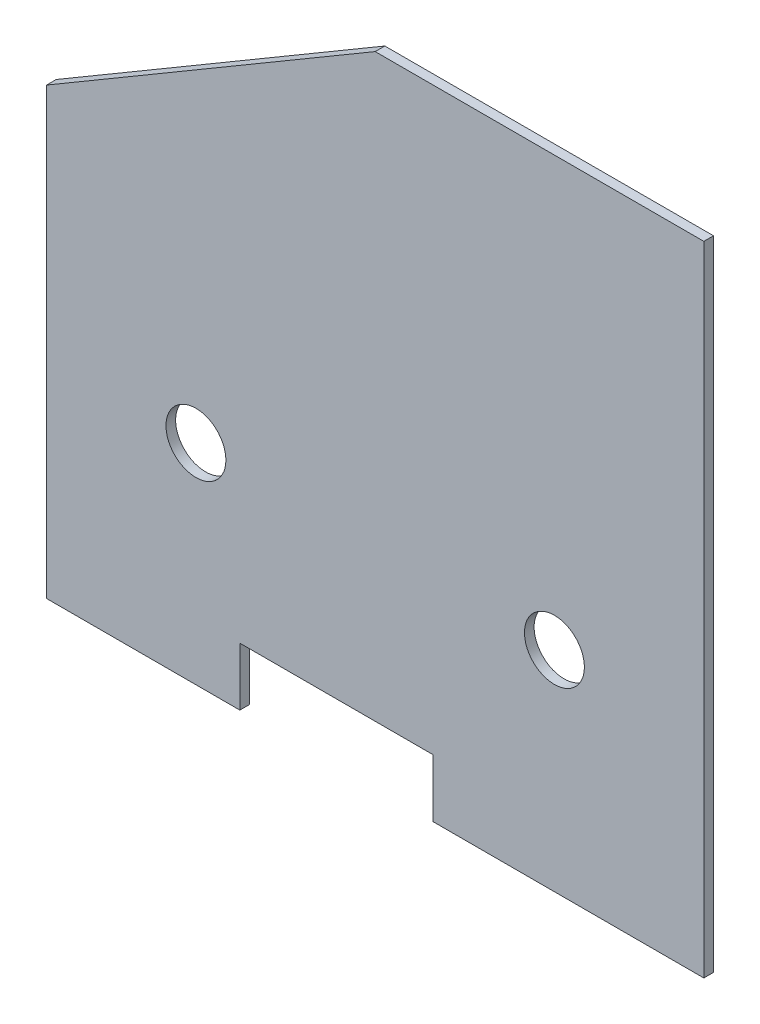
SolidWorks part; units mm, degrees
ref_plane "Front Plane" through (0, 0, 0) normal (0, 0, 1) x (1, 0, 0)
ref_plane "Top Plane" through (0, 0, 0) normal (0, 1, 0) x (1, 0, 0)
ref_plane "Right Plane" through (0, 0, 0) normal (1, 0, 0) x (0, 0, -1)
sketch "Sketch2" plane through (0, 0, 0) normal (0, 0, 1) x (1, 0, 0)
  line L0 (0, 304.8) -> (0, 12.7)
  line L1 (0, 0) -> (431.8, 0) construction
  line L2 (0, 0) -> (0, 431.8) construction
  line L3 (0, 431.8) -> (431.8, 431.8) construction
  line L4 (431.8, 0) -> (431.8, 431.8) construction
  line L5 (0, 304.8) -> (215.9, 431.8)
  line L6 (215.9, 431.8) -> (431.8, 431.8)
  line L7 (0, 12.7) -> (127, 12.7)
  line L8 (127, 12.7) -> (127, 50.8)
  line L9 (254, 50.8) -> (254, 12.7)
  line L10 (254, 50.8) -> (127, 50.8)
  line L11 (254, 12.7) -> (431.8, 12.7)
  line L12 (431.8, 12.7) -> (431.8, 431.8)
  dimension "D1" = 431.8
  dimension "D2" = 431.8
  dimension "D3" = 12.7
  dimension "D4" = 127
  dimension "D6" = 304.8
  dimension "D7" = 215.9
  dimension "D8" = 127
  dimension "D9" = 50.8
extrude "Boss-Extrude1" add sketch "Sketch2" along normal blind 6.35
sketch "Sketch3" plane through (0, 0, 6.35) normal (0, 0, 1) x (1, 0, 0)
  line L0 (98.15, 150.3) -> (333.65, 150.3) construction
  line L1 (0, 12.7) -> (127, 12.7) construction
  line L2 (0, 304.8) -> (0, 12.7) construction
  line L3 (98.15, 150.3) -> (0, 150.3) construction
  line L4 (333.65, 150.3) -> (431.8, 150.3) construction
  line L5 (431.8, 12.7) -> (431.8, 431.8) construction
  circle A0 centre (98.15, 150.3) radius 19.685
  circle A1 centre (333.65, 150.3) radius 19.685
  dimension "D2" = 39.37
  dimension "D1" = 137.6
  dimension "D3" = 98.15
extrude "Cut-Extrude1" cut sketch "Sketch3" against normal through all
